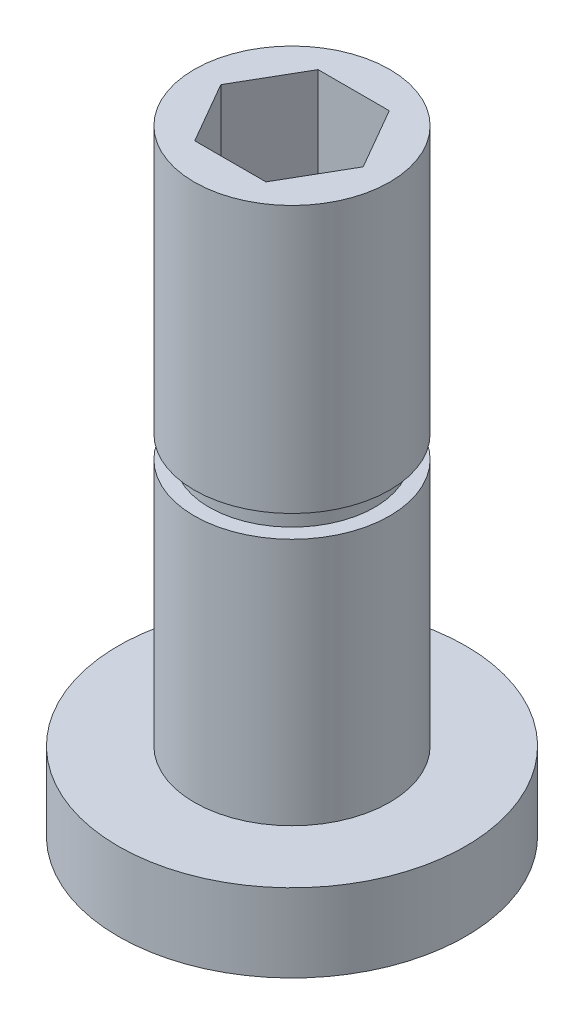
SolidWorks part; units mm, degrees
ref_plane "Front" through (0, 0, 0) normal (0, 0, 1) x (1, 0, 0)
ref_plane "Top" through (0, 0, 0) normal (0, 1, 0) x (1, 0, 0)
ref_plane "Right" through (0, 0, 0) normal (1, 0, 0) x (0, 0, -1)
sketch "Sketch1" plane through (0, 0, 0) normal (0, 1, 0) x (1, 0, 0)
  circle A0 centre (0, 0) radius 8.89
  dimension "D1" = 17.78
extrude "Traingular base (simplified to circle here)" add sketch "Sketch1" along normal blind 4
sketch "Sketch2" plane through (0, 4, 0) normal (0, 1, 0) x (1, 0, 0)
  circle A0 centre (0, 0) radius 5
  dimension "D1" = 10
extrude "Drive shaft" add sketch "Sketch2" along normal blind 27.5
ref_plane "Plane1" through (0, 16.7, 0) normal (0, 1, 0) x (1, 0, 0)
sketch "Sketch4" plane through (0, 16.7, 0) normal (0, 1, 0) x (1, 0, 0)
  circle A0 centre (0, 0) radius 5 construction
  circle A1 centre (0, 0) radius 5
  circle A2 centre (0, 0) radius 4.238
  dimension "D1" = 0.762
extrude "Retaining ring slot" cut sketch "Sketch4" along normal blind 1.143
sketch "Sketch5" plane through (0, 31.5, 0) normal (0, 1, 0) x (1, 0, 0)
  line L1 (3.6449, 0) -> (1.8224, 3.1566)
  line L2 (1.8224, 3.1566) -> (-1.8224, 3.1566)
  line L3 (-1.8224, 3.1566) -> (-3.6449, 0)
  line L4 (-3.6449, 0) -> (-1.8225, -3.1566)
  line L5 (-1.8225, -3.1566) -> (1.8224, -3.1566)
  line L6 (1.8224, -3.1566) -> (3.6449, 0)
  circle A0 centre (0, 0) radius 3.6449 construction
  dimension "D1" = 7.2898
extrude "Hex slot" cut sketch "Sketch5" against normal blind 11.049
